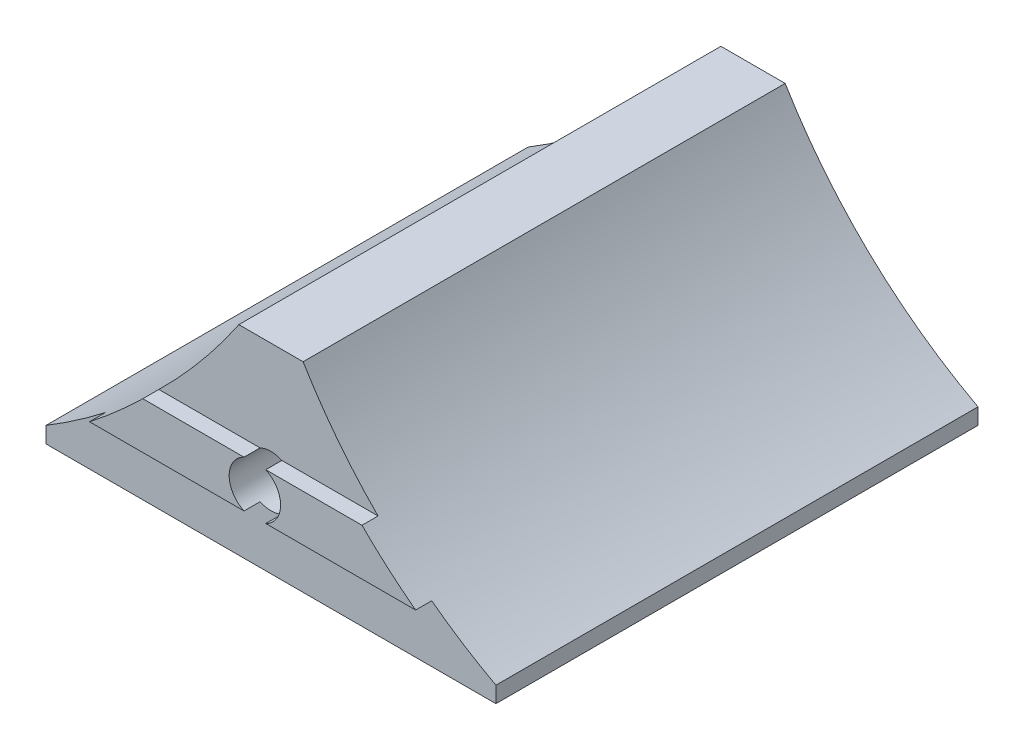
SolidWorks part; units mm, degrees
ref_plane "Front Plane" through (0, 0, 0) normal (0, 0, 1) x (1, 0, 0)
ref_plane "Top Plane" through (0, 0, 0) normal (0, 1, 0) x (1, 0, 0)
ref_plane "Right Plane" through (0, 0, 0) normal (1, 0, 0) x (0, 0, -1)
sketch "Sketch1" plane through (0, 0, 0) normal (0, 0, 1) x (1, 0, 0)
  line L0 (4.0127, 8.0968) -> (4.0127, 9.0968)
  line L1 (16.0127, 20.5287) -> (20.0127, 20.5287)
  line L2 (32.0127, 8.0968) -> (4.0127, 8.0968)
  line L3 (32.0127, 9.0968) -> (32.0127, 8.0968)
  line L4 (-52.2986, 7.3351) -> (-76.4142, 7.3351) construction
  line L5 (-76.4142, 7.3351) -> (-76.4142, -22.6649) construction
  line L6 (-76.4142, -22.6649) -> (23.5858, -22.6649) construction
  line L7 (23.5858, -22.6649) -> (23.5858, 7.3351) construction
  line L8 (23.5858, 7.3351) -> (-0.5299, 7.3351) construction
  line L9 (11.6858, 35.8351) -> (11.6858, 13.4022) construction
  line L10 (23.5858, 7.3351) -> (47.7014, 7.3351) construction
  line L11 (99.4701, 7.3351) -> (121.0133, 7.3351) construction
  line L12 (121.0133, 7.3351) -> (121.0133, -22.6649) construction
  line L13 (121.0133, -22.6649) -> (23.5858, -22.6649) construction
  arc A0 (4.0127, 9.0968) -> (16.0127, 20.5287) centre (-15.9206, 42.0349) ccw
  arc A1 (-52.2986, 7.3351) -> (-0.5299, 7.3351) centre (-26.4142, 35.8351) ccw construction
  circle A2 centre (-26.4142, 35.8351) radius 38.1 construction
  circle A3 centre (73.5858, 35.8351) radius 38.1 construction
  arc A4 (47.7014, 7.3351) -> (99.4701, 7.3351) centre (73.5858, 35.8351) ccw construction
  arc A5 (20.0127, 20.5287) -> (32.0127, 9.0968) centre (46.7065, 36.535) ccw
  point P14 (18.0127, 20.5287)
  point P23 (18.0127, 8.0968)
  dimension "D1" = 38.5
  dimension "D4" = 38.5
  dimension "D5" = 100
  dimension "D8" = 76.2
  dimension "D10" = 100
  dimension "D2" = 28
  dimension "D3" = 1
  dimension "D6" = 28.5
  dimension "D7" = 30
  dimension "D9" = 12.2156
  dimension "D11" = 48.2313
extrude "Main" add sketch "Sketch1" along normal blind 30
sketch "Sketch5" plane through (0, 0, 30) normal (0, 0, 1) x (1, 0, 0)
  line L0 (11.036, 14.5468) -> (24.6774, 14.5468)
  line L1 (7.7187, 11.6468) -> (28.0158, 11.6468)
  line L2 (4.0127, 8.0968) -> (32.0127, 8.0968) construction
  arc A0 (4.0127, 9.0968) -> (16.0127, 20.5287) centre (-15.9206, 42.0349) ccw construction
  arc A1 (20.0127, 20.5287) -> (32.0127, 9.0968) centre (46.7065, 36.535) ccw construction
  arc A2 (11.036, 14.5468) -> (7.7187, 11.6468) centre (-15.9206, 42.0349) cw
  arc A3 (24.6774, 14.5468) -> (28.0158, 11.6468) centre (46.7065, 36.535) ccw
  dimension "D1" = 2.9
  dimension "D2" = 3.55
extrude "Fix" add sketch "Sketch5" along normal blind 1
sketch "Sketch4" plane through (0, 0, 31) normal (0, 0, 1) x (1, 0, 0)
  line L0 (4.0127, 8.0968) -> (32.0127, 8.0968) construction
  line L2 (20.0127, 20.5287) -> (16.0127, 20.5287) construction
  circle A0 centre (18.0127, 13.0968) radius 1.6
  point P7 (18.0127, 20.5287)
  dimension "D1" = 3.2
  dimension "D3" = 5
extrude "FixHole" cut sketch "Sketch4" against normal through all
sketch "Sketch6" plane through (0, 0, 0) normal (0, 0, -1) x (-1, 0, 0)
  circle A0 centre (-18.0127, 13.0968) radius 4.25
  dimension "D1" = 8.5
extrude "FixToolHole" cut sketch "Sketch6" against normal blind 10
